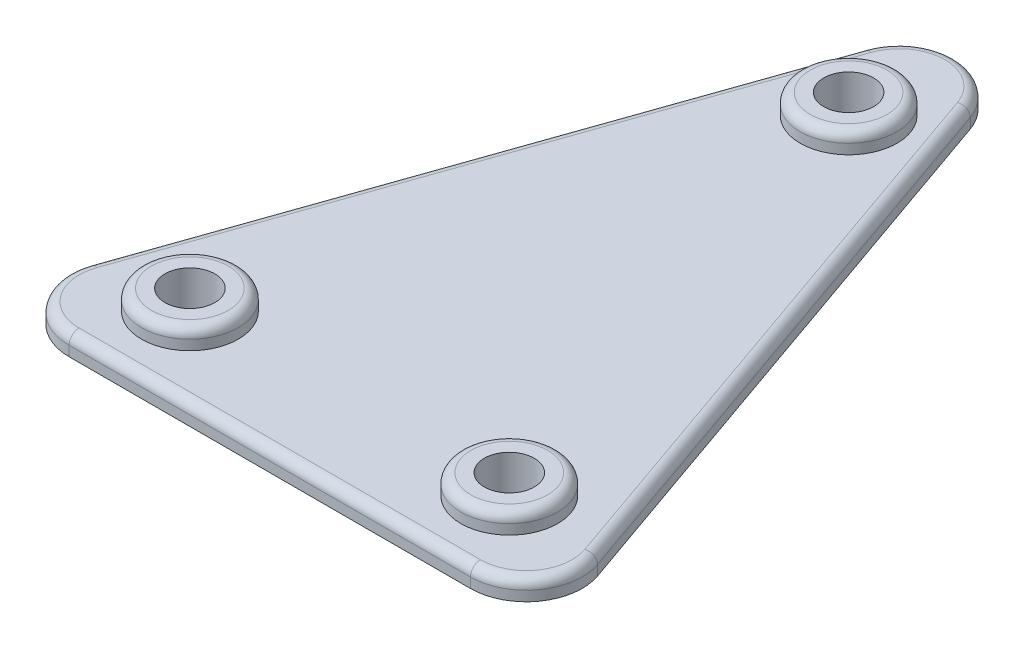
SolidWorks part; units mm, degrees
material "PVC Rigid"
ref_plane "Front Plane" through (0, 0, 0) normal (0, 0, 1) x (1, 0, 0)
ref_plane "Top Plane" through (0, 0, 0) normal (0, 1, 0) x (1, 0, 0)
ref_plane "Right Plane" through (0, 0, 0) normal (1, 0, 0) x (0, 0, -1)
sketch "Sketch1" plane through (0, 0, 0) normal (0, 1, 0) x (1, 0, 0)
  line L0 (14, 0) -> (-14, 0)
  line L1 (-14, 0) -> (0, 40)
  line L2 (0, 0) -> (0, 40) construction
  line L3 (14, 0) -> (0, 40)
  dimension "D1" = 40
  dimension "D2" = 14
extrude "Boss-Extrude1" add sketch "Sketch1" along normal blind 1
sketch "Sketch2" plane through (0, 0, 0) normal (0, 1, 0) x (1, 0, 0)
  line L0 (0, 0) -> (0, 40) construction
  line L1 (-14, 0) -> (14, 0) construction
  circle A0 centre (-8, 4) radius 2.425
  circle A1 centre (0, 29) radius 2.425
  circle A2 centre (8, 4) radius 2.425
  point P12 (0, 0)
  dimension "D1" = 4.85
  dimension "D2" = 4.85
  dimension "D3" = 4
  dimension "D4" = 8
  dimension "D5" = 29
extrude "Boss-Extrude3" add sketch "Sketch2" along normal blind 1 from surface at 1 starting at face at (0, 1, -13.3333)
sketch "Sketch3" plane through (0, 0, 0) normal (0, 1, 0) x (1, 0, 0)
  circle A0 centre (0, 29) radius 1.25
  circle A1 centre (-8, 4) radius 1.25
  circle A2 centre (8, 4) radius 1.25
  dimension "D1" = 2.5
  dimension "D2" = 2.5
  dimension "D3" = 2.5
extrude "Cut-Extrude2" cut sketch "Sketch3" against normal through all and the other way through all
fillet "Fillet2" radius 2.8 3 edges at (0, 0.5, -40) (14, 0.5, 0) (-14, 0.5, 0)
fillet "Fillet3" radius 0.5 9 edges at (0, 1, -34.3242) (7.6695, 1, -18.0871) (12.3371, 1, -1.1798) (0, 1, 0) (-12.3371, 1, -1.1798) (-7.6695, 1, -18.0871) (8, 2, -1.575) (-8, 2, -1.575) (0, 2, -26.575)
